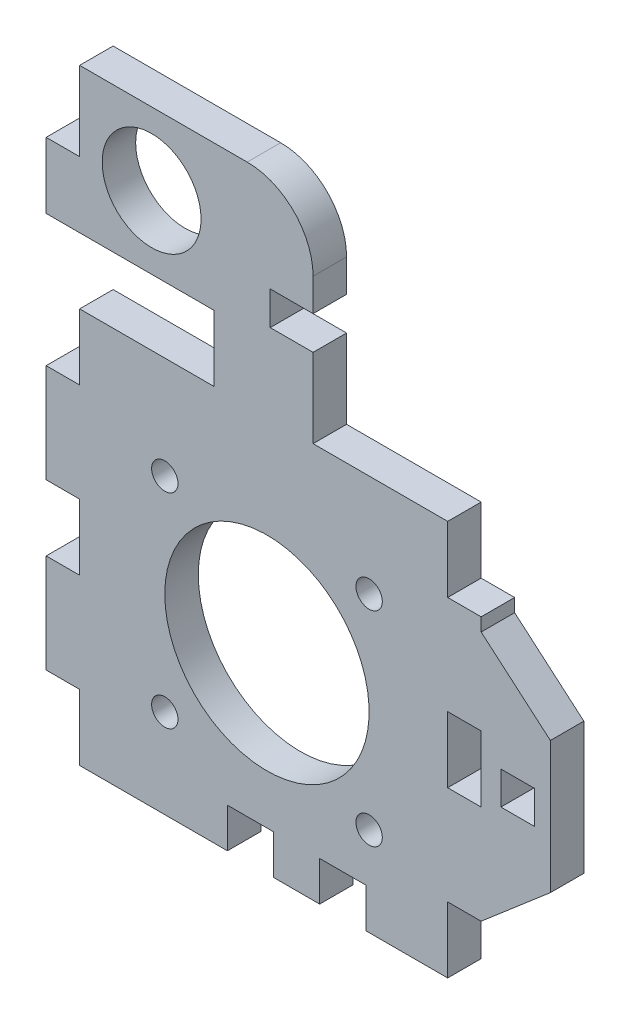
SolidWorks part; units mm, degrees
ref_plane "Front Plane" through (0, 0, 0) normal (0, 0, 1) x (1, 0, 0)
ref_plane "Top Plane" through (0, 0, 0) normal (0, 1, 0) x (1, 0, 0)
ref_plane "Right Plane" through (0, 0, 0) normal (1, 0, 0) x (0, 0, -1)
sketch "Sketch1" plane through (0, 0, 0) normal (0, 0, 1) x (1, 0, 0)
  line L0 (32.5, 19) -> (43, 10)
  line L1 (-15.5, -15.5) -> (15.5, -15.5) construction
  line L2 (-15.5, -15.5) -> (-15.5, 15.5) construction
  line L3 (-15.5, 15.5) -> (15.5, 15.5) construction
  line L4 (15.5, -15.5) -> (15.5, 15.5) construction
  line L5 (-15.5, -15.5) -> (15.5, 15.5) construction
  line L6 (-15.5, 15.5) -> (15.5, -15.5) construction
  line L7 (-33.5, -29) -> (32.5, -29)
  line L8 (-33.5, -29) -> (-33.5, 31)
  line L9 (-33.5, 31) -> (32.5, 31)
  line L10 (32.5, -29) -> (32.5, -19)
  line L11 (-21, -21) -> (21, -21) construction
  line L12 (-21, -21) -> (-21, 21) construction
  line L13 (-21, 21) -> (21, 21) construction
  line L14 (21, -21) -> (21, 21) construction
  line L15 (-21, -21) -> (21, 21) construction
  line L16 (-21, 21) -> (21, -21) construction
  line L17 (43, 10) -> (43, -10)
  line L18 (43, -10) -> (32.5, -19)
  line L19 (-33.5, 0) -> (25.5, 0) construction
  line L20 (32.5, 19) -> (32.5, 31)
  point P0 (0, 0)
  point P10 (0, 0)
  dimension "D1" = 12.5
  dimension "D2" = 31
  dimension "D3" = 17
  dimension "D4" = 42
  dimension "D5" = 10
  dimension "D6" = 8
  dimension "D7" = 43
  dimension "D8" = 10
  dimension "D9" = 20
extrude "Boss-Extrude1" add sketch "Sketch1" along normal blind 5.08 contours L9 L20 L0 L17 L18 L10 L7 L8
sketch "Sketch2" plane through (0, 0, 0) normal (0, 0, -1) x (-1, 0, 0)
  line L0 (15.5, 15.5) -> (-15.5, 15.5) construction
  line L1 (-4.5, 21) -> (-4.5, -21) construction
  line L2 (21, 21) -> (-21, 21) construction
  line L3 (21, -21) -> (-21, -21) construction
  line L4 (33.5, -29) -> (-32.5, -29) construction
  line L5 (-8, -29) -> (-15, -29)
  line L6 (-8, -29) -> (-8, -23)
  line L7 (-8, -23) -> (-15, -23)
  line L8 (-15, -29) -> (-15, -23)
  line L9 (-1, -29) -> (-8, -29) construction
  line L10 (6, -29) -> (-1, -29)
  line L11 (6, -29) -> (6, -23)
  line L12 (6, -23) -> (-1, -23)
  line L13 (-1, -29) -> (-1, -23)
  line L15 (-35.5, -2.5) -> (-40.58, -2.5)
  line L16 (-35.5, -2.5) -> (-35.5, 2.5)
  line L17 (-35.5, 2.5) -> (-40.58, 2.5)
  line L18 (-40.58, -2.5) -> (-40.58, 2.5)
  line L19 (-35.5, -2.5) -> (-40.58, 2.5) construction
  line L20 (-35.5, 2.5) -> (-40.58, -2.5) construction
  circle A0 centre (0, 0) radius 15.5
  circle A1 centre (15.5, -15.5) radius 2
  circle A2 centre (-15.5, -15.5) radius 2
  circle A3 centre (-15.5, 15.5) radius 2
  circle A4 centre (15.5, 15.5) radius 2
  point P33 (-4.5, -29)
  point P34 (-38.04, 0)
  dimension "D1" = 4
  dimension "D2" = 4.5
  dimension "D3" = 6
  dimension "D4" = 7
  dimension "D5" = 7
  dimension "D6" = 5.08
  dimension "D7" = 35.5
  dimension "D8" = 5
extrude "Cut-Extrude1" cut sketch "Sketch2" against normal through all
sketch "Sketch4" plane through (0, 0, 5.08) normal (0, 0, 1) x (1, 0, 0)
  line L0 (32.5, 6) -> (27.42, 6)
  line L1 (32.5, -29) -> (27.42, -29)
  line L2 (32.5, -29) -> (32.5, -19)
  line L3 (32.5, -19) -> (27.42, -19)
  line L4 (27.42, -29) -> (27.42, -19)
  line L5 (27.42, -4) -> (27.42, 6)
  line L6 (32.5, -4) -> (32.5, 6)
  line L7 (32.5, -4) -> (27.42, -4)
  line L8 (32.5, 31) -> (27.42, 31)
  line L9 (27.42, 21) -> (27.42, 31)
  line L10 (32.5, 21) -> (32.5, 31)
  line L11 (32.5, 21) -> (27.42, 21)
  line L13 (-33.5, -29) -> (-28.42, -29)
  line L14 (-33.5, -29) -> (-33.5, -19)
  line L15 (-33.5, -19) -> (-28.42, -19)
  line L16 (-28.42, -29) -> (-28.42, -19)
  line L17 (-33.5, -4) -> (-28.42, -4)
  line L18 (-33.5, -4) -> (-33.5, 6)
  line L19 (-33.5, 6) -> (-28.42, 6)
  line L20 (-28.42, -4) -> (-28.42, 6)
  line L21 (-33.5, 21) -> (-28.42, 21)
  line L22 (-33.5, 21) -> (-33.5, 31)
  line L23 (-33.5, 31) -> (-28.42, 31)
  line L24 (-28.42, 21) -> (-28.42, 31)
  dimension "D1" = 5.08
  dimension "D2" = 10
  dimension "D3" = 3
extrude "Cut-Extrude2" cut sketch "Sketch4" against normal through all
sketch "Sketch5" plane through (0, 0, 5.08) normal (0, 0, 1) x (1, 0, 0)
  line L0 (-28.42, 31) -> (27.42, 31) construction
  line L1 (-8, 63) -> (7, 63)
  line L2 (-8, 41) -> (-8, 31)
  line L3 (-8, 31) -> (7, 31)
  line L4 (7, 63) -> (7, 31)
  line L5 (-8, 63) -> (7, 31) construction
  line L6 (-8, 31) -> (7, 63) construction
  line L7 (-0.5, 31) -> (-0.5, -23) construction
  line L8 (-6, -23) -> (1, -23) construction
  line L9 (-33.5, 6) -> (-33.5, 21) construction
  line L10 (-8, 63) -> (-33.5, 63)
  line L12 (-8, 41) -> (-33.5, 41)
  line L13 (-33.5, 63) -> (-33.5, 41)
  line L14 (-33.5, 21) -> (-28.42, 21) construction
  circle A1 centre (-17.5, 52) radius 7.5
  point P0 (-0.5, 47)
  dimension "D4" = 15
  dimension "D6" = 16
  dimension "D1" = 15
  dimension "D2" = 32
  dimension "D3" = 20
  dimension "D5" = 21
extrude "Boss-Extrude2" add sketch "Sketch5" against normal up to surface (5.08 mm away) up to face at (0.9133, -6.4074, 0)
sketch "Sketch6" plane through (0, 0, 5.08) normal (0, 0, 1) x (1, 0, 0)
  line L0 (-28.42, 21) -> (-28.42, 31) construction
  line L1 (-33.5, 63) -> (-28.42, 63)
  line L2 (-33.5, 63) -> (-33.5, 51)
  line L3 (-33.5, 51) -> (-28.42, 51)
  line L4 (-28.42, 63) -> (-28.42, 51)
  line L5 (-33.5, 41) -> (-8, 41) construction
  line L6 (1, -29) -> (8, -29) construction
  line L7 (0.5, 43) -> (8.5, 43)
  line L8 (0.5, 43) -> (0.5, 48.08)
  line L9 (0.5, 48.08) -> (8.5, 48.08)
  line L10 (8.5, 43) -> (8.5, 48.08)
  line L11 (0.5, 43) -> (8.5, 48.08) construction
  line L12 (0.5, 48.08) -> (8.5, 43) construction
  line L13 (7, 31) -> (27.42, 31) construction
  point P9 (4.5, 45.54)
  point P14 (4.5, -29)
  dimension "D1" = 10
  dimension "D2" = 5.08
  dimension "D3" = 8
  dimension "D4" = 12
extrude "Cut-Extrude3" cut sketch "Sketch6" against normal through all
fillet "Fillet1" radius 10 1 edges at (7, 63, 2.54)
equation "\"pulley_pitch_diam\"= 12.73mm"
equation "\"pulley_total_width\"= 16mm"
equation "\"pulley_total_diam\"= 16mm"
equation "\"belt_width\"= 6mm"
equation "\"material_thickness\"= 3mm"
equation "\"shaft_diam\"= 8mm"
equation "\"bearing_od\"= 22mm"
equation "\"bearing_thickness\"= 7mm"
